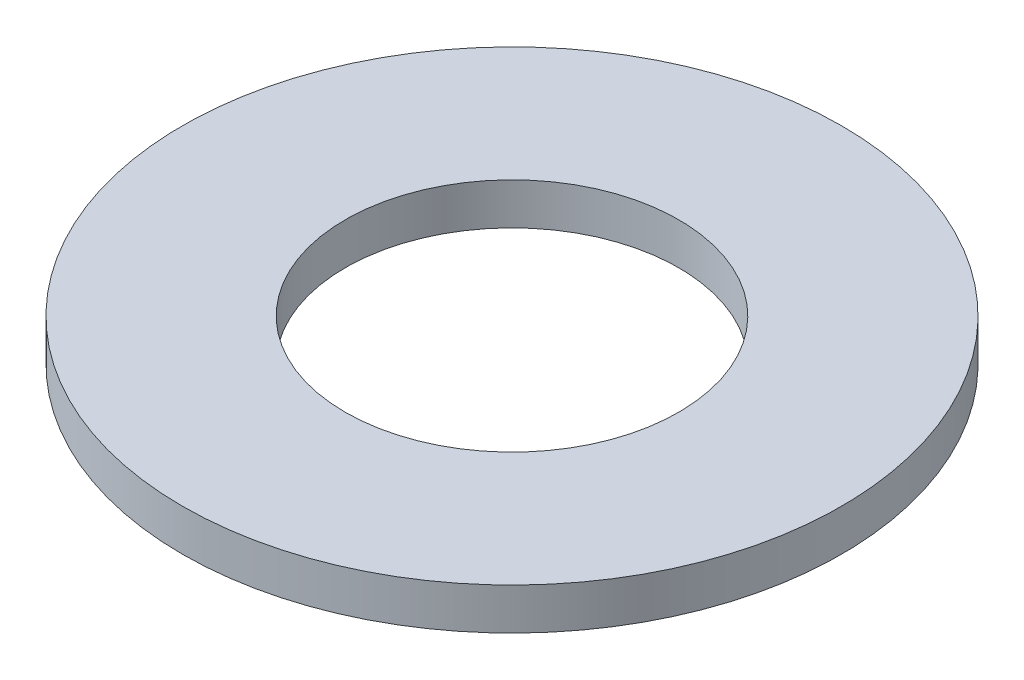
SolidWorks part; units mm, degrees
material "Alum Plate"
ref_plane "Front Plane" through (0, 0, 0) normal (0, 0, 1) x (1, 0, 0)
ref_plane "Top Plane" through (0, 0, 0) normal (0, 1, 0) x (1, 0, 0)
ref_plane "Right Plane" through (0, 0, 0) normal (1, 0, 0) x (0, 0, -1)
other "Bounding Box"
ref_plane "Default Plane" through (0, 2.286, 19.05) normal (0, -1, 0) x (-1, 0, 0)
sketch "Sketch1" plane through (0, 0, 0) normal (0, 1, 0) x (1, 0, 0)
  circle A0 centre (0, 0) radius 6.4135
  circle A1 centre (0, 0) radius 12.6746
  dimension "D1" = 25.3492
  dimension "D2" = 12.827
extrude "Boss-Extrude1" add sketch "Sketch1" along normal mid plane 1.6002
equation "\"Unit Measure\"= \"BoundingVolume\" / \"Thickness\"'in^2"
